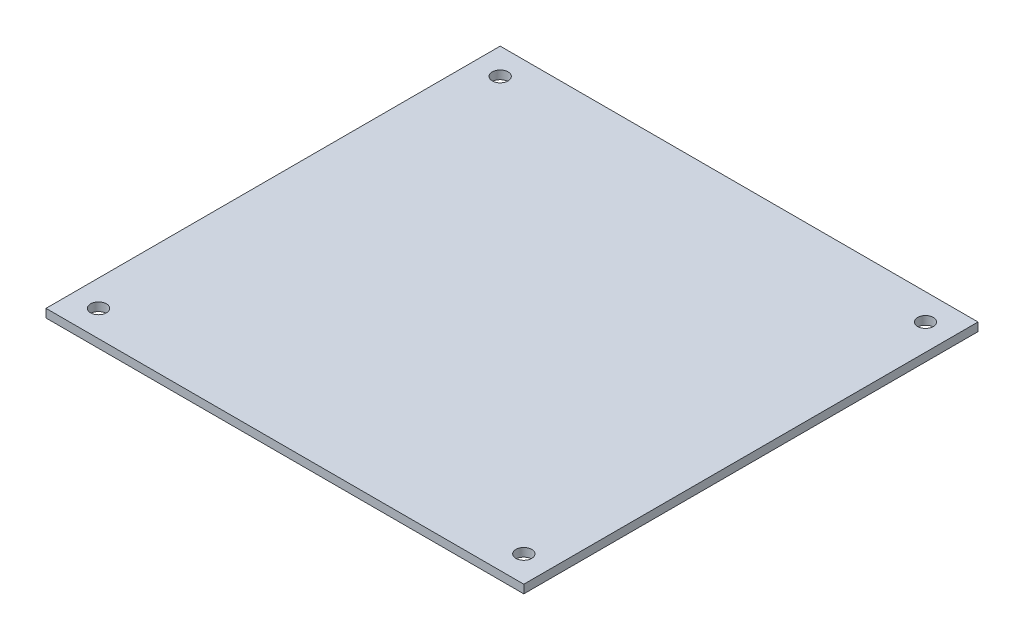
SolidWorks part; units mm, degrees
ref_plane "Front Plane" through (0, 0, 0) normal (0, 0, 1) x (1, 0, 0)
ref_plane "Top Plane" through (0, 0, 0) normal (0, 1, 0) x (1, 0, 0)
ref_plane "Right Plane" through (0, 0, 0) normal (1, 0, 0) x (0, 0, -1)
sketch "Sketch2" plane through (0, 0, 0) normal (0, 1, 0) x (1, 0, 0)
  line L4 (0, 0) -> (0, 86.5)
  line L5 (0, 86.5) -> (91, 86.5)
  line L6 (91, 86.5) -> (91, 0)
  line L7 (91, 0) -> (0, 0)
  line L8 (0, 86.5) -> (6, 86.5) construction
  line L9 (6, 86.5) -> (6, 0) construction
  line L10 (91, 86.5) -> (85, 86.5) construction
  line L11 (85, 86.5) -> (85, 0) construction
  dimension "D1" = 86.5
  dimension "D2" = 91
  dimension "D3" = 6
  dimension "D4" = 6
extrude "PCB" add sketch "Sketch2" along normal blind 1.6
sketch "Sketch3" plane through (0, 1.6, 0) normal (0, 1, 0) x (1, 0, 0)
  line L0 (5, 81.5) -> (5, 5)
  line L5 (0, 86.5) -> (91, 0) construction
  line L6 (0, 0) -> (91, 86.5) construction
  line L7 (5, 5) -> (86, 5)
  line L8 (86, 81.5) -> (86, 5)
  line L9 (5, 81.5) -> (86, 81.5)
  circle A0 centre (5, 81.5) radius 1.5
  circle A1 centre (86, 81.5) radius 1.5
  circle A2 centre (5, 5) radius 1.5
  circle A3 centre (86, 5) radius 1.5
  point P0 (45.5, 43.25)
extrude "Cut-Extrude1" cut sketch "Sketch3" against normal blind 10 contours L0 A2 L7 | L7 A3 L8 | L8 A3 L7 | L7 A2 L0 | L8 A1 L9 | L9 A0 L0 | L0 A0 L9 | L9 A1 L8
